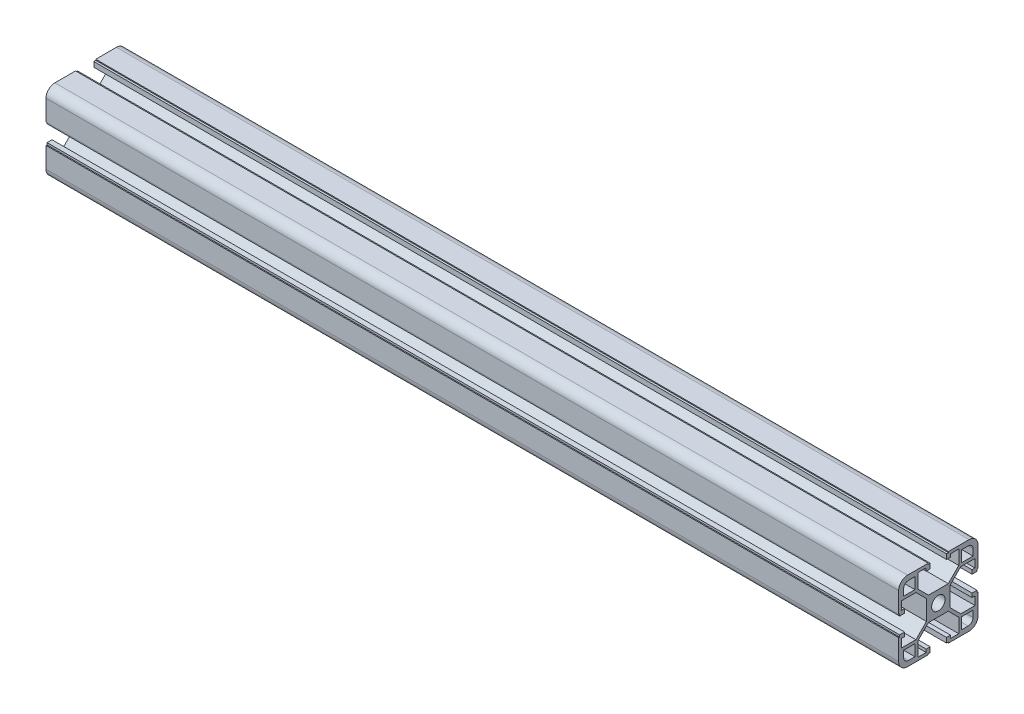
SolidWorks part; units mm, degrees
ref_plane "前视基准面" through (0, 0, 0) normal (0, 0, 1) x (1, 0, 0)
ref_plane "上视基准面" through (0, 0, 0) normal (0, 1, 0) x (1, 0, 0)
ref_plane "右视基准面" through (0, 0, 0) normal (1, 0, 0) x (0, 0, -1)
sketch "草图1" plane through (0, 0, 0) normal (0, 1, 0) x (1, 0, 0)
  line L0 (-215, 0) -> (215, 0)
  line L1 (0, 101.9544) -> (0, -23.3477) construction
  dimension "D1" = 430
  dimension "D2" = 215
other "铝型材 40 X 40L X R4.5(1)"
ref_plane "基准面1" through (-215, 0, 0) normal (1, 0, 0) x (0, 0, -1)
sketch "Sketch1" plane through (-215, 0, 0) normal (1, 0, 0) x (0, 0, -1)
  line L0 (-5.1, 20) -> (-5.1, 19.5)
  line L1 (-5.1, 19.5) -> (-4.1, 19.5)
  line L2 (-4.1, 19.5) -> (-4.1, 17)
  line L3 (-6.1, 18.5) -> (-10.3, 18.5)
  line L4 (-15.5, -20) -> (-5.1, -20)
  line L5 (-20, -15.5) -> (-20, -5.1)
  line L6 (15.5, 20) -> (5.1, 20)
  line L7 (20, 15.5) -> (20, 5.1)
  line L8 (0, 14.8756) -> (0, 0) construction
  line L9 (0, 0) -> (14.1675, 0) construction
  line L10 (-10.3, 18.5) -> (-10.3, 11.3)
  line L11 (-10.3, 11.3) -> (-5, 6)
  line L12 (-5, 6) -> (5, 6)
  line L13 (10.3, 11.3) -> (5, 6)
  line L14 (10.3, 18.5) -> (10.3, 11.3)
  line L15 (6.1, 18.5) -> (10.3, 18.5)
  line L16 (4.1, 19.5) -> (4.1, 17)
  line L17 (5.1, 19.5) -> (4.1, 19.5)
  line L18 (5.1, 20) -> (5.1, 19.5)
  line L19 (-5.1, 20) -> (-15.5, 20)
  line L20 (20, 5.1) -> (19.5, 5.1)
  line L21 (11.8, 17.5) -> (15, 17.5)
  line L22 (11.8, 17.5) -> (11.8, 11.8)
  line L23 (11.8, 11.8) -> (17.5, 11.8)
  line L24 (17.5, 15) -> (17.5, 11.8)
  line L25 (19.5, 5.1) -> (19.5, 4.1)
  line L26 (19.5, 4.1) -> (17, 4.1)
  line L27 (17, 6.1) -> (17, 4.1)
  line L28 (18.5, 6.1) -> (17, 6.1)
  line L29 (18.5, 6.1) -> (18.5, 10.3)
  line L30 (18.5, 10.3) -> (11.3, 10.3)
  line L31 (11.3, 10.3) -> (6, 5)
  line L32 (6, 5) -> (6, -5)
  line L33 (11.3, -10.3) -> (6, -5)
  line L34 (18.5, -10.3) -> (11.3, -10.3)
  line L35 (18.5, -6.1) -> (18.5, -10.3)
  line L36 (18.5, -6.1) -> (17, -6.1)
  line L37 (17, -4.1) -> (17, -6.1)
  line L38 (19.5, -4.1) -> (17, -4.1)
  line L39 (19.5, -5.1) -> (19.5, -4.1)
  line L40 (20, -5.1) -> (19.5, -5.1)
  line L41 (5.1, -20) -> (5.1, -19.5)
  line L42 (5.1, -19.5) -> (4.1, -19.5)
  line L43 (4.1, -19.5) -> (4.1, -17)
  line L44 (6.1, -17) -> (4.1, -17)
  line L45 (6.1, -18.5) -> (6.1, -17)
  line L46 (6.1, -18.5) -> (10.3, -18.5)
  line L47 (10.3, -18.5) -> (10.3, -11.3)
  line L48 (10.3, -11.3) -> (5, -6)
  line L49 (5, -6) -> (-5, -6)
  line L50 (-10.3, -11.3) -> (-5, -6)
  line L51 (-10.3, -18.5) -> (-10.3, -11.3)
  line L52 (-6.1, -18.5) -> (-10.3, -18.5)
  line L53 (-6.1, -18.5) -> (-6.1, -17)
  line L54 (-4.1, -17) -> (-6.1, -17)
  line L55 (-4.1, -19.5) -> (-4.1, -17)
  line L56 (-5.1, -19.5) -> (-4.1, -19.5)
  line L57 (-5.1, -20) -> (-5.1, -19.5)
  line L58 (-20, -5.1) -> (-19.5, -5.1)
  line L59 (5.1, -20) -> (15.5, -20)
  line L60 (-20, 5.1) -> (-20, 15.5)
  line L61 (-19.5, -5.1) -> (-19.5, -4.1)
  line L62 (-6.1, 18.5) -> (-6.1, 17)
  line L63 (-6.1, 17) -> (-4.1, 17)
  line L64 (6.1, 18.5) -> (6.1, 17)
  line L65 (4.1, 17) -> (6.1, 17)
  line L66 (-19.5, -4.1) -> (-17, -4.1)
  line L67 (-15, 17.5) -> (-11.8, 17.5)
  line L68 (-17.5, 15) -> (-17.5, 11.8)
  line L69 (-17.5, 11.8) -> (-11.8, 11.8)
  line L70 (-11.8, 17.5) -> (-11.8, 11.8)
  line L71 (-17, -6.1) -> (-17, -4.1)
  line L72 (-18.5, -6.1) -> (-17, -6.1)
  line L73 (-18.5, -6.1) -> (-18.5, -10.3)
  line L74 (-18.5, -10.3) -> (-11.3, -10.3)
  line L75 (-11.3, -10.3) -> (-6, -5)
  line L76 (-6, -5) -> (-6, 5)
  line L77 (-11.3, 10.3) -> (-6, 5)
  line L78 (-18.5, 10.3) -> (-11.3, 10.3)
  line L79 (-18.5, 6.1) -> (-18.5, 10.3)
  line L80 (-18.5, 6.1) -> (-17, 6.1)
  line L81 (-17, 4.1) -> (-17, 6.1)
  line L82 (-19.5, 4.1) -> (-17, 4.1)
  line L83 (-19.5, 5.1) -> (-19.5, 4.1)
  line L84 (-20, 5.1) -> (-19.5, 5.1)
  line L85 (20, -5.1) -> (20, -15.5)
  line L87 (-17.5, -11.8) -> (-11.8, -11.8)
  line L88 (-17.5, -11.8) -> (-17.5, -15)
  line L89 (-15, -17.5) -> (-11.8, -17.5)
  line L90 (-11.8, -11.8) -> (-11.8, -17.5)
  line L91 (11.8, -11.8) -> (17.5, -11.8)
  line L92 (11.8, -11.8) -> (11.8, -17.5)
  line L93 (11.8, -17.5) -> (15, -17.5)
  line L94 (17.5, -11.8) -> (17.5, -15)
  circle A0 centre (0, 0) radius 3.4
  arc A1 (-20, 15.5) -> (-15.5, 20) centre (-15.5, 15.5) cw
  arc A2 (20, 15.5) -> (15.5, 20) centre (15.5, 15.5) ccw
  arc A3 (-15.5, -20) -> (-20, -15.5) centre (-15.5, -15.5) cw
  arc A4 (15.5, -20) -> (20, -15.5) centre (15.5, -15.5) ccw
  arc A5 (-15, 17.5) -> (-17.5, 15) centre (-15, 15) ccw
  arc A6 (17.5, 15) -> (15, 17.5) centre (15, 15) ccw
  arc A7 (17.5, -15) -> (15, -17.5) centre (15, -15) cw
  arc A8 (-17.5, -15) -> (-15, -17.5) centre (-15, -15) ccw
  point P2 (0, 10)
  point P4 (0, 0)
  point P5 (-20, -20)
  point P6 (20, -20)
  point P7 (20, 20)
  point P8 (-20, 20)
  point P36 (-20, 20)
  point P39 (20, 20)
  point P121 (0, 0)
  dimension "D1" = 20.6
  dimension "D2" = 40
  dimension "D3" = 8.2
  dimension "D4" = 10.2
  dimension "D5" = 14
  dimension "D6" = 6.8
  dimension "D7" = 4.5
  dimension "D8" = 45
  dimension "D12" = 2.5
  dimension "D13" = 5.7
  dimension "D14" = 1.5
  dimension "D18" = 2.5
  dimension "D19" = 2.5
  dimension "D15" = 2.5
  dimension "D9" = 0.5
  dimension "D10" = 1.5
  dimension "D11" = 10
  dimension "D16" = 3
  dimension "D17" = 2
  dimension "D20" = 1.5
  dimension "D21" = 2.5
sketch "草图2" plane through (0, 20, 0) normal (0, 1, 0) x (1, 0, 0)
  line L0 (0, 86.1779) -> (0, -55.3806) construction
  line L2 (-60.2995, 0) -> (128.123, 0) construction
  circle A0 centre (-1, 0) radius 2.5
  circle A1 centre (108, 0) radius 2.5
  dimension "D1" = 5
  dimension "D2" = 1
  dimension "D3" = 5
  dimension "D4" = 109
extrude "切除-拉伸1" cut sketch "草图2" against normal through all
